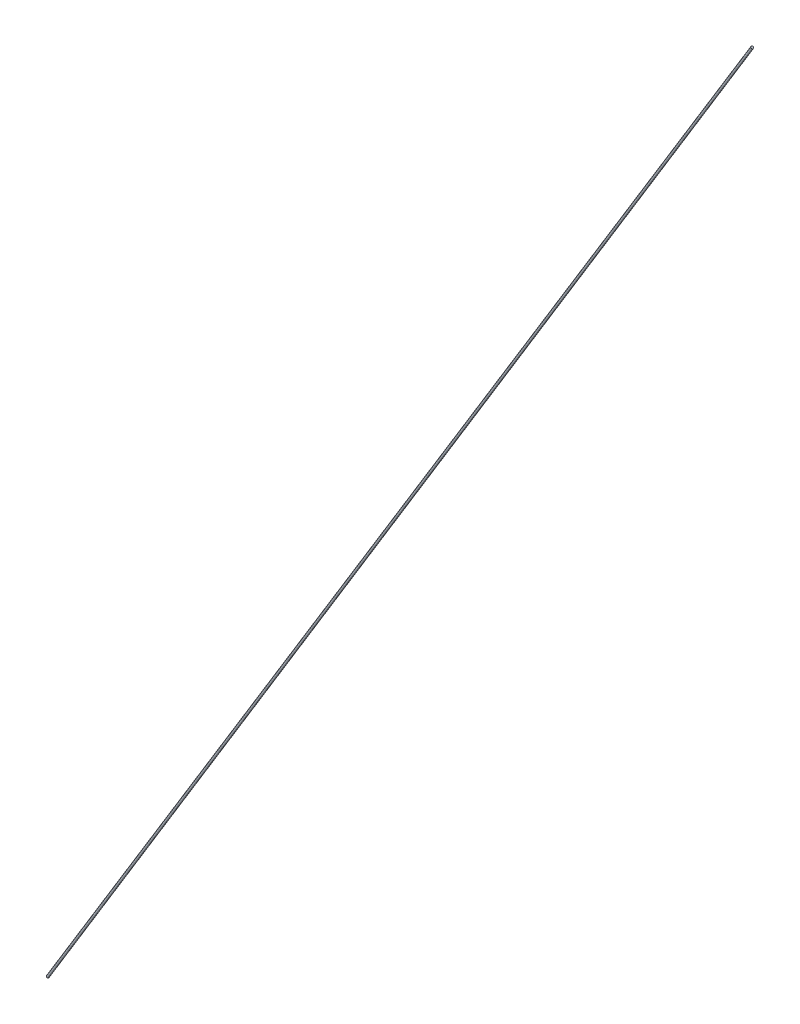
SolidWorks part; units mm, degrees
ref_plane "前视基准面" through (0, 0, 0) normal (0, 0, 1) x (1, 0, 0)
ref_plane "上视基准面" through (0, 0, 0) normal (0, 1, 0) x (1, 0, 0)
ref_plane "右视基准面" through (0, 0, 0) normal (1, 0, 0) x (0, 0, -1)
sketch "草图2" plane through (0, 0, 0) normal (0, 0, 1) x (1, 0, 0)
  line L6 (307.5, 505) -> (0, 0)
sweep "扫描1" add path "草图2" circular profile diameter 1 parameters "D3"=1
